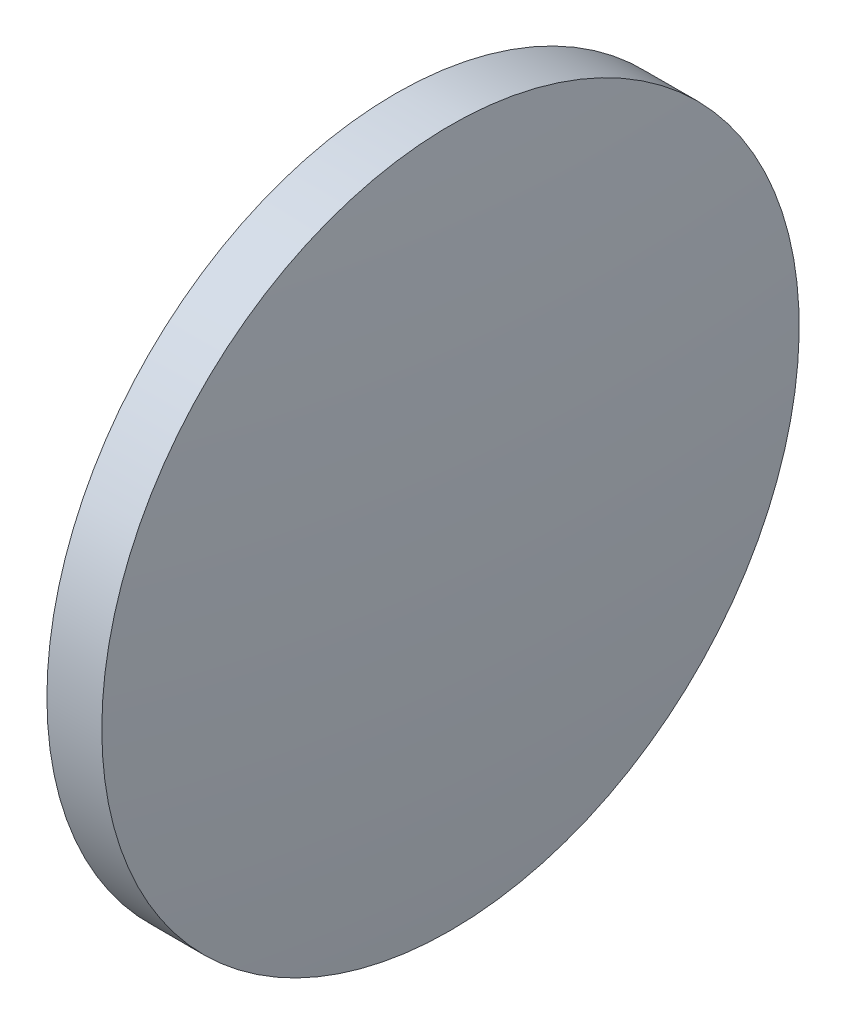
SolidWorks part; units mm, degrees
ref_plane "前视基准面" through (0, 0, 0) normal (0, 0, 1) x (1, 0, 0)
ref_plane "上视基准面" through (0, 0, 0) normal (0, 1, 0) x (1, 0, 0)
ref_plane "右视基准面" through (0, 0, 0) normal (1, 0, 0) x (0, 0, -1)
sketch "草图1" plane through (0, 0, 0) normal (0, 0, 1) x (1, 0, 0)
  line L0 (79.3054, 48.6161) -> (93.4772, 48.6161) construction
  line L1 (85.4585, 61.3161) -> (87.4579, 61.3161)
  line L2 (87.4579, 61.3161) -> (87.4579, 35.9161)
  line L3 (87.4579, 35.9161) -> (85.4585, 35.9161)
  line L4 (85.4585, 35.9161) -> (85.4585, 61.3161)
  arc A0 (85.4585, 61.3161) -> (85.4585, 35.9161) centre (219.5297, 48.6161) ccw
  arc A1 (87.4579, 35.9161) -> (87.4579, 61.3161) centre (-46.6133, 48.6161) ccw
  dimension "D1" = 25.4
  dimension "D2" = 1.9993
revolve "旋转1" add sketch "草图1" angle 360 about L0
